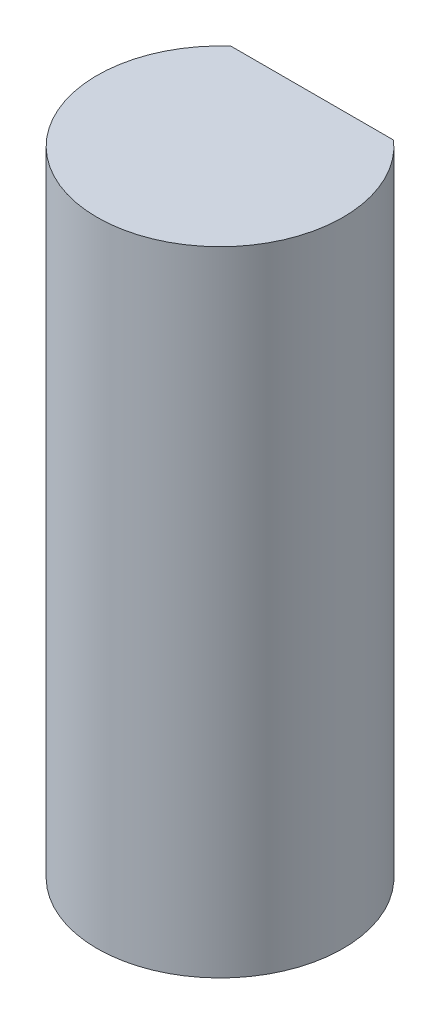
SolidWorks part; units mm, degrees
ref_plane "Face" through (0, 0, 0) normal (0, 0, 1) x (1, 0, 0)
ref_plane "Dessus" through (0, 0, 0) normal (0, 1, 0) x (1, 0, 0)
ref_plane "Droite" through (0, 0, 0) normal (1, 0, 0) x (0, 0, -1)
sketch "Esquisse1" plane through (0, 0, 0) normal (0, 1, 0) x (1, 0, 0)
  circle A0 centre (0, 0) radius 4
  dimension "D1" = 8
extrude "Extrusion1" add sketch "Esquisse1" along normal blind 20.6
sketch "Esquisse2" plane through (0, 20.6, 0) normal (0, 1, 0) x (1, 0, 0)
  line L0 (-2.6458, 3) -> (2.6458, 3)
  line L1 (0, 4) -> (5.8103, 4) construction
  circle A0 centre (0, 0) radius 4 construction
  arc A1 (-2.6458, 3) -> (2.6458, 3) centre (0, 0) cw
  dimension "D1" = 1
extrude "Enlèv. mat.-Extru.1" cut sketch "Esquisse2" against normal blind 10
